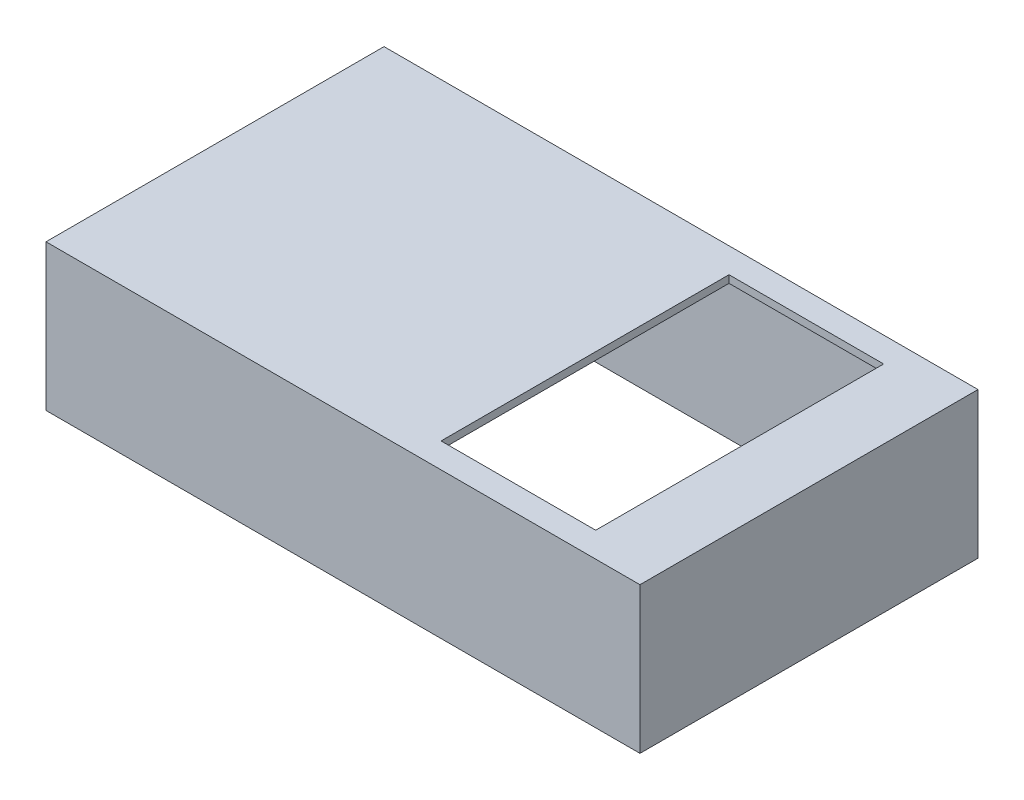
SolidWorks part; units mm, degrees
ref_plane "Front Plane" through (0, 0, 0) normal (0, 0, 1) x (1, 0, 0)
ref_plane "Top Plane" through (0, 0, 0) normal (0, 1, 0) x (1, 0, 0)
ref_plane "Right Plane" through (0, 0, 0) normal (1, 0, 0) x (0, 0, -1)
sketch "Sketch1" plane through (0, 0, 0) normal (0, 1, 0) x (1, 0, 0)
  line L1 (0, 0) -> (55.7, 0)
  line L2 (0, 0) -> (0, 31.7)
  line L3 (0, 31.7) -> (55.7, 31.7)
  line L4 (55.7, 0) -> (55.7, 31.7)
  dimension "D1" = 55.7
  dimension "D2" = 31.7
extrude "Boss-Extrude1" add sketch "Sketch1" along normal blind 13.7
sketch "Sketch2" plane through (0, 13.7, 0) normal (0, 1, 0) x (1, 0, 0)
  line L0 (55.7, 0) -> (55.7, 31.7) construction
  line L1 (34.7, 29.35) -> (49.2, 29.35)
  line L2 (34.7, 29.35) -> (34.7, 2.35)
  line L3 (34.7, 2.35) -> (49.2, 2.35)
  line L4 (49.2, 29.35) -> (49.2, 2.35)
  line L5 (55.7, 31.7) -> (0, 31.7) construction
  dimension "D1" = 6.5
  dimension "D2" = 27
  dimension "D3" = 14.5
  dimension "D4" = 2.35
extrude "Cut-Extrude1" cut sketch "Sketch2" against normal blind 13.7
sketch "Sketch3" plane through (0, 0, 0) normal (0, -1, 0) x (1, 0, 0)
  line L0 (0, -31.7) -> (0, 0) construction
  line L1 (2, -2) -> (53.7, -2)
  line L2 (2, -2) -> (2, -29.7)
  line L3 (2, -29.7) -> (53.7, -29.7)
  line L4 (53.7, -2) -> (53.7, -29.7)
  line L5 (0, 0) -> (55.7, 0) construction
  line L6 (55.7, -31.7) -> (0, -31.7) construction
  line L8 (55.7, 0) -> (55.7, -31.7) construction
  dimension "D1" = 2
  dimension "D2" = 2
  dimension "D3" = 2
  dimension "D4" = 2
extrude "Cut-Extrude2" cut sketch "Sketch3" against normal blind 13
